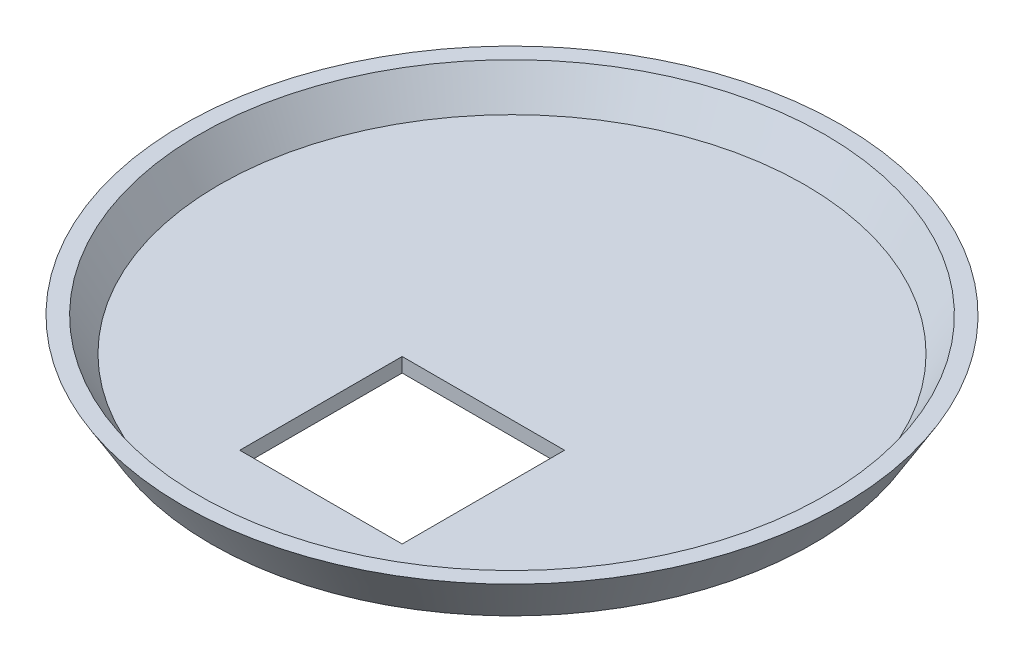
SolidWorks part; units mm, degrees
ref_plane "Front Plane" through (0, 0, 0) normal (0, 0, 1) x (1, 0, 0)
ref_plane "Top Plane" through (0, 0, 0) normal (0, 1, 0) x (1, 0, 0)
ref_plane "Right Plane" through (0, 0, 0) normal (1, 0, 0) x (0, 0, -1)
sketch "Sketch1" plane through (0, 0, 0) normal (0, 0, 1) x (1, 0, 0)
  line L0 (0, 0) -> (63, 0)
  line L1 (63, 0) -> (69, 10)
  line L6 (0, 3) -> (61.3014, 3)
  line L7 (61.3014, 3) -> (65.5014, 10)
  line L8 (69, 10) -> (65.5014, 10)
  line L9 (0, 0) -> (0, 3)
  line L10 (61.3014, 3) -> (66.4275, 11.5435) construction
  dimension "D1" = 69
  dimension "D2" = 63
  dimension "D3" = 10
  dimension "D4" = 3
revolve "Revolve1" add sketch "Sketch1" angle 360 about L9
sketch "Sketch2" plane through (0, 0, 0) normal (0, -1, 0) x (1, 0, 0)
  line L1 (-11, 46) -> (23, 46)
  line L2 (-11, 46) -> (-11, 12)
  line L3 (-11, 12) -> (23, 12)
  line L4 (23, 46) -> (23, 12)
  dimension "D1" = 34
  dimension "D2" = 34
  dimension "D3" = 11
  dimension "D4" = 12
extrude "Cut-Extrude1" cut sketch "Sketch2" against normal through all
